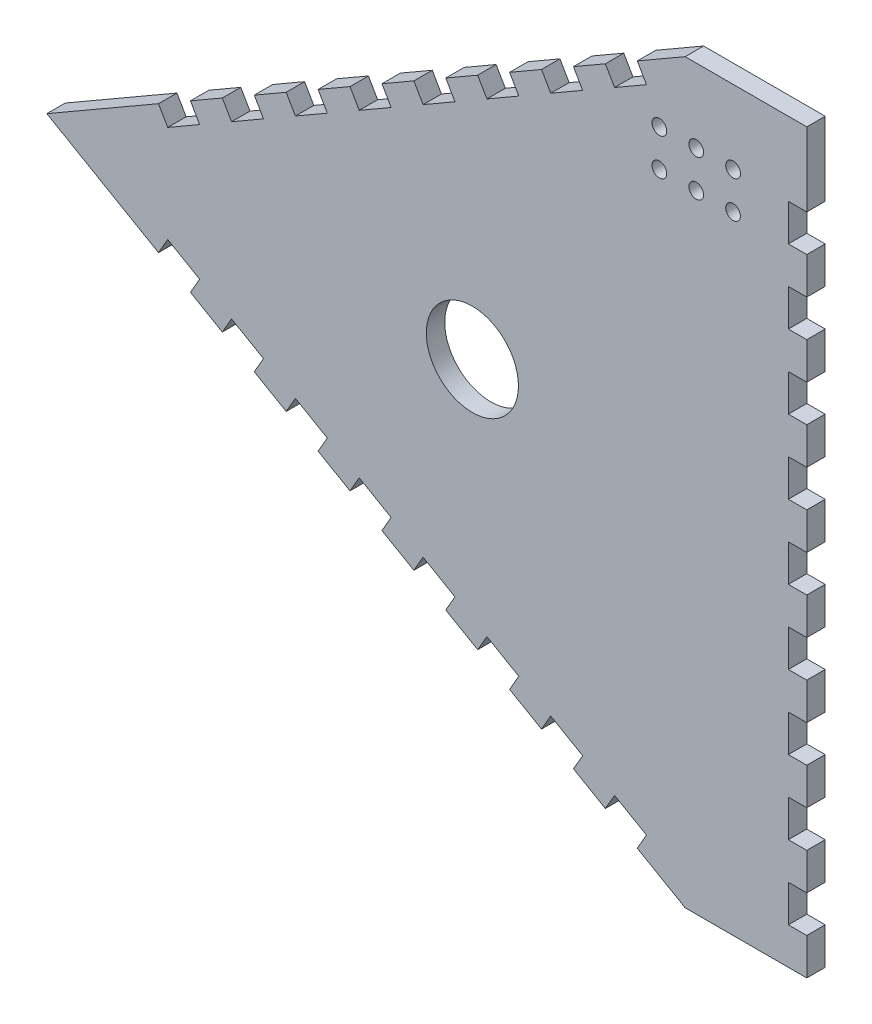
SolidWorks part; units mm, degrees
ref_plane "Front Plane" through (0, 0, 0) normal (0, 0, 1) x (1, 0, 0)
ref_plane "Top Plane" through (0, 0, 0) normal (0, 1, 0) x (1, 0, 0)
ref_plane "Right Plane" through (0, 0, 0) normal (1, 0, 0) x (0, 0, -1)
sketch "Sketch1" plane through (0, 0, 0) normal (0, 0, 1) x (1, 0, 0)
  line L0 (2.5, 0) -> (-30.5, 0)
  line L1 (2.5, 0) -> (-30.5, 0)
  line L2 (2.5, 0) -> (2.5, -200)
  line L3 (2.5, -200) -> (-30.5, -200)
  line L4 (-17.5, -20) -> (-27.5, -20) construction
  line L5 (-203.7051, -100) -> (-30.5, 0)
  line L7 (-30.5, -200) -> (-203.7051, -100)
  line L8 (-201.1315, -101.4859) -> (2.5, -100) construction
  line L9 (-2.5, 0) -> (2.5, 0)
  line L10 (2.5, 0) -> (-2.5, 0)
  line L15 (2.5, 0) -> (-2.5, 0)
  circle A0 centre (-17.5, -20) radius 2
  circle A1 centre (-27.5, -20) radius 2
  circle A2 centre (-37.5, -20) radius 2
  circle A3 centre (-27.5, -30) radius 2
  circle A4 centre (-37.5, -30) radius 2
  circle A5 centre (-17.5, -30) radius 2
  dimension "D8" = 4
  dimension "D2" = 60
  dimension "D3" = 200
  dimension "D4" = 188.4551
  dimension "D5" = 200
  dimension "D11" = 10
  dimension "D9" = 3
  dimension "D10" = 2
extrude "Boss-Extrude1" add sketch "Sketch1" along normal blind 5
sketch "Sketch2" plane through (0, 0, 5) normal (0, 0, 1) x (1, 0, 0)
  line L3 (-2.5, -100) -> (-136.8791, -100) construction
  point P13 (2.5, -100.4557)
sketch "Sketch3" plane through (0, 0, 5) normal (0, 0, 1) x (1, 0, 0)
  line L0 (-121.4327, -52.5) -> (-112.7724, -47.5)
  line L1 (-112.7724, -47.5) -> (-110.2724, -51.8301)
  line L2 (-110.2724, -51.8301) -> (-118.9327, -56.8301)
  line L3 (-118.9327, -56.8301) -> (-121.4327, -52.5)
  line L4 (-101.6122, -46.8301) -> (-104.1122, -42.5)
  line L5 (-92.9519, -41.8301) -> (-101.6122, -46.8301)
  line L6 (-95.4519, -37.5) -> (-92.9519, -41.8301)
  line L7 (-104.1122, -42.5) -> (-95.4519, -37.5)
  line L8 (-84.2917, -36.8301) -> (-86.7917, -32.5)
  line L9 (-75.6314, -31.8301) -> (-84.2917, -36.8301)
  line L10 (-78.1314, -27.5) -> (-75.6314, -31.8301)
  line L11 (-86.7917, -32.5) -> (-78.1314, -27.5)
  line L12 (-66.9711, -26.8301) -> (-69.4711, -22.5)
  line L13 (-58.3109, -21.8301) -> (-66.9711, -26.8301)
  line L14 (-60.8109, -17.5) -> (-58.3109, -21.8301)
  line L15 (-69.4711, -22.5) -> (-60.8109, -17.5)
  line L16 (-49.6506, -16.8301) -> (-52.1506, -12.5)
  line L17 (-40.9904, -11.8301) -> (-49.6506, -16.8301)
  line L18 (-43.4904, -7.5) -> (-40.9904, -11.8301)
  line L19 (-52.1506, -12.5) -> (-43.4904, -7.5)
  line L20 (-136.2532, -66.8301) -> (-138.7532, -62.5)
  line L21 (-127.5929, -61.8301) -> (-136.2532, -66.8301)
  line L22 (-130.0929, -57.5) -> (-127.5929, -61.8301)
  line L23 (-138.7532, -62.5) -> (-130.0929, -57.5)
  line L24 (-153.5737, -76.8301) -> (-156.0737, -72.5)
  line L25 (-144.9134, -71.8301) -> (-153.5737, -76.8301)
  line L26 (-147.4134, -67.5) -> (-144.9134, -71.8301)
  line L27 (-156.0737, -72.5) -> (-147.4134, -67.5)
  line L28 (-170.8942, -86.8301) -> (-173.3942, -82.5)
  line L29 (-162.2339, -81.8301) -> (-170.8942, -86.8301)
  line L30 (-164.7339, -77.5) -> (-162.2339, -81.8301)
  line L31 (-173.3942, -82.5) -> (-164.7339, -77.5)
  line L32 (-30.5, 0) -> (-117.1025, -150) construction
  line L33 (-30.5, -200) -> (-117.1025, -50) construction
  line L36 (-203.7051, -100) -> (-2.5, -100) construction
  line L39 (-112.7724, -152.5) -> (-110.2724, -148.1699)
  line L40 (-110.2724, -148.1699) -> (-118.9327, -143.1699)
  line L41 (-173.3942, -117.5) -> (-164.7339, -122.5)
  line L42 (-164.7339, -122.5) -> (-162.2339, -118.1699)
  line L43 (-156.0737, -127.5) -> (-147.4134, -132.5)
  line L44 (-147.4134, -132.5) -> (-144.9134, -128.1699)
  line L45 (-144.9134, -128.1699) -> (-153.5737, -123.1699)
  line L46 (-153.5737, -123.1699) -> (-156.0737, -127.5)
  line L47 (-138.7532, -137.5) -> (-130.0929, -142.5)
  line L48 (-130.0929, -142.5) -> (-127.5929, -138.1699)
  line L49 (-127.5929, -138.1699) -> (-136.2532, -133.1699)
  line L50 (-136.2532, -133.1699) -> (-138.7532, -137.5)
  line L55 (-162.2339, -118.1699) -> (-170.8942, -113.1699)
  line L56 (-170.8942, -113.1699) -> (-173.3942, -117.5)
  line L57 (-52.1506, -187.5) -> (-43.4904, -192.5)
  line L58 (-43.4904, -192.5) -> (-40.9904, -188.1699)
  line L59 (-40.9904, -188.1699) -> (-49.6506, -183.1699)
  line L60 (-49.6506, -183.1699) -> (-52.1506, -187.5)
  line L61 (-69.4711, -177.5) -> (-60.8109, -182.5)
  line L62 (-60.8109, -182.5) -> (-58.3109, -178.1699)
  line L63 (-58.3109, -178.1699) -> (-66.9711, -173.1699)
  line L64 (-66.9711, -173.1699) -> (-69.4711, -177.5)
  line L65 (-86.7917, -167.5) -> (-78.1314, -172.5)
  line L66 (-78.1314, -172.5) -> (-75.6314, -168.1699)
  line L67 (-75.6314, -168.1699) -> (-84.2917, -163.1699)
  line L68 (-84.2917, -163.1699) -> (-86.7917, -167.5)
  line L69 (-104.1122, -157.5) -> (-95.4519, -162.5)
  line L70 (-95.4519, -162.5) -> (-92.9519, -158.1699)
  line L71 (-92.9519, -158.1699) -> (-101.6122, -153.1699)
  line L72 (-101.6122, -153.1699) -> (-104.1122, -157.5)
  line L73 (-118.9327, -143.1699) -> (-121.4327, -147.5)
  line L74 (-121.4327, -147.5) -> (-112.7724, -152.5)
  line L75 (-2.5, -80) -> (-2.5, -90)
  line L76 (-2.5, -100) -> (2.5, -100)
  line L77 (-2.5, -100) -> (-2.5, -110)
  line L78 (-2.5, -110) -> (2.5, -110)
  line L79 (2.5, -100) -> (2.5, -110)
  line L80 (-2.5, -80) -> (2.5, -80)
  line L81 (2.5, -80) -> (2.5, -90)
  line L82 (-2.5, -90) -> (2.5, -90)
  line L83 (-2.5, -60) -> (-2.5, -70)
  line L84 (-2.5, -60) -> (2.5, -60)
  line L85 (2.5, -60) -> (2.5, -70)
  line L86 (-2.5, -70) -> (2.5, -70)
  line L87 (-2.5, -40) -> (-2.5, -50)
  line L88 (-2.5, -40) -> (2.5, -40)
  line L89 (2.5, -40) -> (2.5, -50)
  line L90 (-2.5, -50) -> (2.5, -50)
  line L91 (-2.5, -20) -> (-2.5, -30)
  line L92 (-2.5, -20) -> (2.5, -20)
  line L93 (2.5, -20) -> (2.5, -30)
  line L94 (-2.5, -30) -> (2.5, -30)
  line L99 (-2.5, -120) -> (-2.5, -130)
  line L100 (-2.5, -120) -> (2.5, -120)
  line L101 (2.5, -120) -> (2.5, -130)
  line L102 (-2.5, -130) -> (2.5, -130)
  line L103 (-2.5, -140) -> (-2.5, -150)
  line L104 (-2.5, -140) -> (2.5, -140)
  line L105 (2.5, -140) -> (2.5, -150)
  line L106 (-2.5, -150) -> (2.5, -150)
  line L107 (-2.5, -160) -> (-2.5, -170)
  line L108 (-2.5, -160) -> (2.5, -160)
  line L109 (2.5, -160) -> (2.5, -170)
  line L110 (-2.5, -170) -> (2.5, -170)
  line L111 (-2.5, -180) -> (-2.5, -190)
  line L112 (-2.5, -180) -> (2.5, -180)
  line L113 (2.5, -180) -> (2.5, -190)
  line L114 (-2.5, -190) -> (2.5, -190)
  line L129 (-179.5544, -91.8301) -> (-188.2147, -96.8301) [skipped]
  line L130 (-182.0544, -87.5) -> (-179.5544, -91.8301) [skipped]
  line L131 (-188.2147, -96.8301) -> (-190.7147, -92.5) [skipped]
  line L132 (-190.7147, -92.5) -> (-182.0544, -87.5) [skipped]
  line L133 (-2.5, 0) -> (2.5, 0) [skipped]
  line L134 (2.5, 0) -> (2.5, -10) [skipped]
  line L135 (-2.5, 0) -> (-2.5, -10) [skipped]
  line L136 (-2.5, -10) -> (2.5, -10) [skipped]
  circle A0 centre (-88.235, -100) radius 12.5
  point P15 (-151.7436, -130)
  point P16 (-134.423, -140)
  point P23 (-169.0641, -120)
  point P24 (-186.3846, -110)
  point P29 (-47.8205, -190)
  point P46 (-117.1025, -50)
  point P52 (-99.782, -40)
  point P57 (-82.4615, -30)
  point P62 (-65.141, -20)
  point P67 (-47.8205, -10)
  point P72 (-134.423, -60)
  point P77 (-151.7436, -70)
  point P82 (-169.0641, -80)
  point P87 (-186.3846, -90)
  point P91 (-65.141, -180)
  point P92 (-82.4615, -170)
  point P93 (-99.782, -160)
  point P94 (-117.1025, -150)
  point P116 (-147.4134, -100)
  dimension "D8" = 25
  dimension "D2" = 5
  dimension "D3" = 10
  dimension "D4" = 5
  dimension "D5" = 10
  dimension "D6" = 5
  dimension "D1" = 6
  dimension "D7" = 5
extrude "Cut-Extrude5" cut sketch "Sketch3" against normal through all both and the other way through all
sketch "Sketch5" plane through (0, 0, 5) normal (0, 0, 1) x (1, 0, 0)
  line L0 (-44.1167, -149.1961) -> (-44.1167, -50.6417) construction
  text T0 "EU4M" font "Century Gothic" height in points 72
  point P6 (-44.1167, -99.9189)
